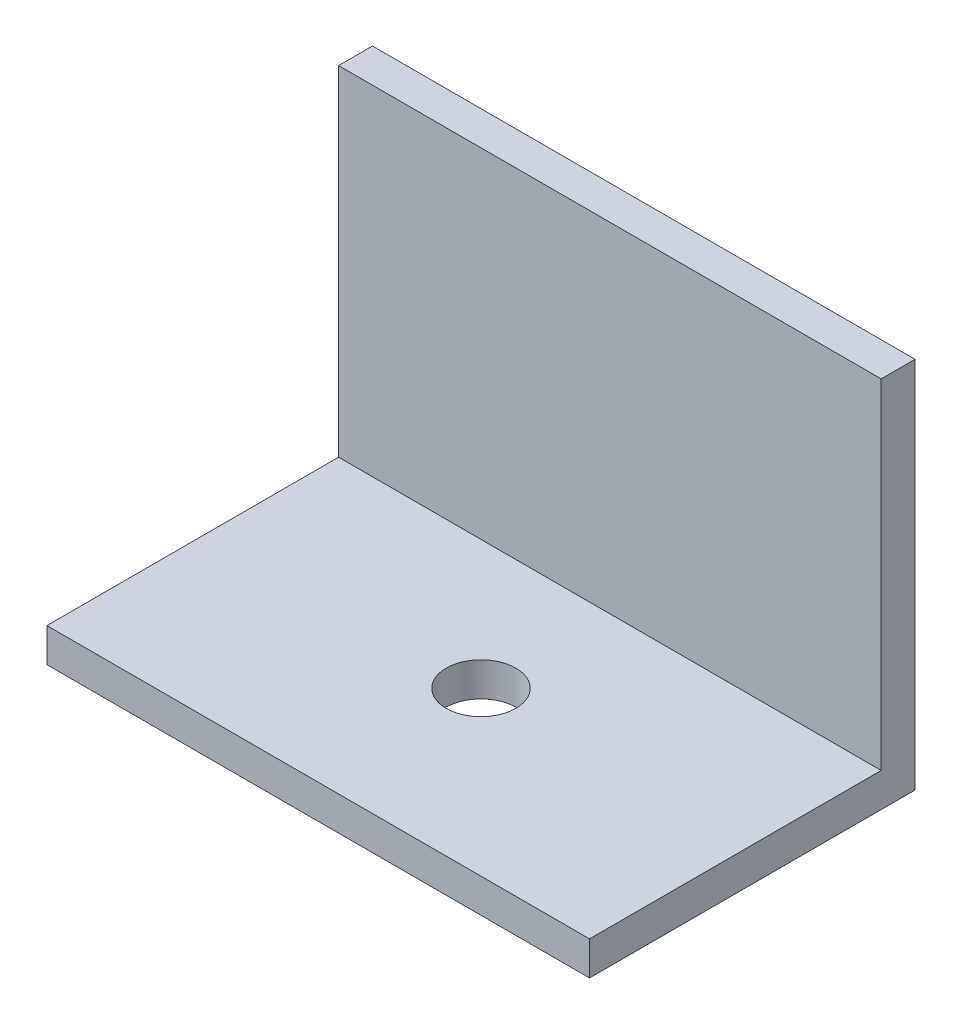
SolidWorks part; units mm, degrees
ref_plane "Front Plane" through (0, 0, 0) normal (0, 0, 1) x (1, 0, 0)
ref_plane "Top Plane" through (0, 0, 0) normal (0, 1, 0) x (1, 0, 0)
ref_plane "Right Plane" through (0, 0, 0) normal (1, 0, 0) x (0, 0, -1)
sketch "Sketch1" plane through (0, 0, 0) normal (0, 1, 0) x (1, 0, 0)
  line L1 (-25.4, 15.24) -> (25.4, 15.24)
  line L2 (-25.4, 15.24) -> (-25.4, -15.24)
  line L3 (-25.4, -15.24) -> (25.4, -15.24)
  line L4 (25.4, 15.24) -> (25.4, -15.24)
  line L5 (-25.4, 15.24) -> (25.4, -15.24) construction
  line L6 (-25.4, -15.24) -> (25.4, 15.24) construction
  point P0 (0, 0)
  dimension "D1" = 30.48
  dimension "D2" = 50.8
extrude "Boss-Extrude1" add sketch "Sketch1" along normal blind 3.175
sketch "Sketch2" plane through (0, 3.175, 0) normal (0, 1, 0) x (1, 0, 0)
  line L0 (25.4, -15.24) -> (25.4, 15.24) construction
  line L1 (-25.4, 15.24) -> (25.4, 15.24)
  line L2 (-25.4, 15.24) -> (-25.4, 12.065)
  line L3 (-25.4, 12.065) -> (25.4, 12.065)
  line L4 (25.4, 15.24) -> (25.4, 12.065)
  line L5 (-25.4, 15.24) -> (25.4, 12.065) construction
  line L6 (-25.4, 12.065) -> (25.4, 15.24) construction
  line L7 (25.4, 15.24) -> (-25.4, 15.24) construction
  point P0 (0, 13.6525)
  point P7 (0, 0)
  point P9 (0, 12.5156)
  dimension "D1" = 3.175
extrude "Boss-Extrude2" add sketch "Sketch2" along normal blind 31.75
sketch "Sketch3" plane through (0, 0, 0) normal (0, -1, 0) x (1, 0, 0)
  circle A0 centre (0, 0) radius 3.2639
  point P5 (0, 0)
  dimension "D1" = 6.5278
extrude "Cut-Extrude1" cut sketch "Sketch3" against normal blind 50.8
